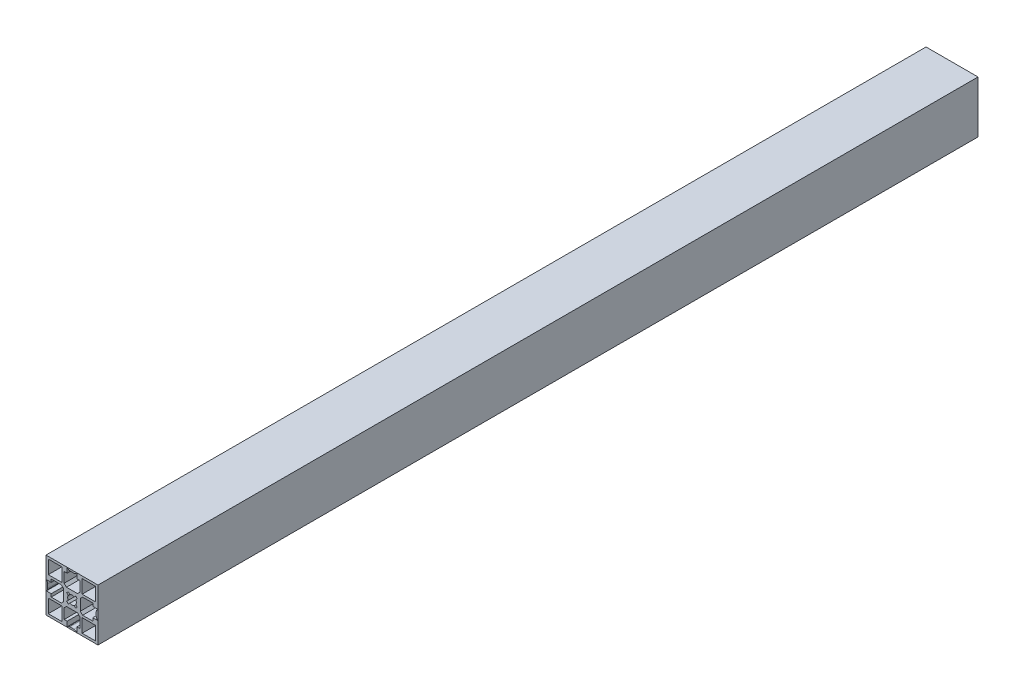
SolidWorks part; units mm, degrees
material "6061 Alloy"
ref_plane "Front Plane" through (0, 0, 0) normal (0, 0, 1) x (1, 0, 0)
ref_plane "Top Plane" through (0, 0, 0) normal (0, 1, 0) x (1, 0, 0)
ref_plane "Right Plane" through (0, 0, 0) normal (1, 0, 0) x (0, 0, -1)
sketch "Sketch1" plane through (0, 0, 0) normal (0, 0, 1) x (1, 0, 0)
  line L8 (-22.4995, -22.5007) -> (22.5005, -22.5007)
  line L9 (22.5005, -22.5007) -> (22.5005, 22.4993)
  line L10 (22.5005, 22.4993) -> (-22.4995, 22.4993)
  line L11 (-22.4995, 22.4993) -> (-22.4995, -22.5007)
  line L24 (-20.4995, -20.5007) -> (-20.4995, -8.8007)
  line L25 (-8.7996, -20.5007) -> (-20.4995, -20.5007)
  line L26 (-8.7996, -8.8007) -> (-8.7996, -20.5007)
  line L27 (-20.4995, -8.8007) -> (-8.7996, -8.8007)
  line L28 (8.8005, -20.5008) -> (8.8005, -8.8008)
  line L29 (20.5005, -20.5008) -> (8.8005, -20.5008)
  line L30 (20.5005, -8.8008) -> (20.5005, -20.5008)
  line L31 (8.8005, -8.8008) -> (20.5005, -8.8008)
  line L32 (20.5006, 8.7993) -> (8.8006, 8.7993)
  line L33 (20.5006, 20.4993) -> (20.5006, 8.7993)
  line L34 (8.8006, 20.4993) -> (20.5006, 20.4993)
  line L35 (8.8006, 8.7993) -> (8.8006, 20.4993)
  line L36 (-8.7995, 20.4993) -> (-8.7995, 8.7993)
  line L37 (-8.7995, 8.7993) -> (-20.4995, 8.7993)
  line L38 (-20.4995, 8.7993) -> (-20.4995, 20.4993)
  line L39 (-20.4995, 20.4993) -> (-8.7995, 20.4993)
  line L54 (-22.1995, -3.9507) -> (-21.7318, -3.483)
  line L55 (-22.1995, -4.2507) -> (-22.1995, -3.9507)
  line L56 (-17.9995, -4.2507) -> (-22.1995, -4.2507)
  line L57 (-17.9995, -6.8007) -> (-17.9995, -4.2507)
  line L58 (-9.1995, -6.8007) -> (-17.9995, -6.8007)
  line L59 (-7.1995, -4.8007) -> (-9.1995, -6.8007)
  line L60 (-7.1995, 4.7993) -> (-7.1995, -4.8007)
  line L61 (-9.1995, 6.7993) -> (-7.1995, 4.7993)
  line L62 (-17.9995, 6.7993) -> (-9.1995, 6.7993)
  line L63 (-17.9995, 4.2493) -> (-17.9995, 6.7993)
  line L64 (-22.1995, 4.2493) -> (-17.9995, 4.2493)
  line L65 (-22.1995, 3.9493) -> (-22.1995, 4.2493)
  line L66 (-21.7317, 3.4815) -> (-22.1995, 3.9493)
  line L67 (-20.9995, -1.7152) -> (-20.9995, 1.7137)
  line L82 (-6.7995, -18.0007) -> (-6.7995, -9.2007)
  line L83 (-4.2495, -18.0007) -> (-6.7995, -18.0007)
  line L84 (-4.2495, -22.2007) -> (-4.2495, -18.0007)
  line L85 (-3.9495, -22.2007) -> (-4.2495, -22.2007)
  line L86 (-3.4817, -21.733) -> (-3.9495, -22.2007)
  line L87 (1.715, -21.0007) -> (-1.7139, -21.0007)
  line L88 (3.9505, -22.2007) -> (3.4828, -21.733)
  line L89 (4.2505, -22.2007) -> (3.9505, -22.2007)
  line L90 (4.2505, -18.0007) -> (4.2505, -22.2007)
  line L91 (6.8005, -18.0007) -> (4.2505, -18.0007)
  line L92 (6.8005, -9.2007) -> (6.8005, -18.0007)
  line L93 (4.8005, -7.2007) -> (6.8005, -9.2007)
  line L94 (-4.7995, -7.2007) -> (4.8005, -7.2007)
  line L95 (-6.7995, -9.2007) -> (-4.7995, -7.2007)
  line L110 (7.2005, -4.8007) -> (7.2005, 4.7993)
  line L111 (9.2005, -6.8007) -> (7.2005, -4.8007)
  line L112 (18.0005, -6.8007) -> (9.2005, -6.8007)
  line L113 (18.0005, -4.2507) -> (18.0005, -6.8007)
  line L114 (22.2005, -4.2507) -> (18.0005, -4.2507)
  line L115 (22.2005, -3.9507) -> (22.2005, -4.2507)
  line L116 (21.7327, -3.4829) -> (22.2005, -3.9507)
  line L117 (21.0005, 1.7138) -> (21.0005, -1.7151)
  line L118 (22.2005, 3.9493) -> (21.7328, 3.4816)
  line L119 (22.2005, 4.2493) -> (22.2005, 3.9493)
  line L120 (18.0005, 4.2493) -> (22.2005, 4.2493)
  line L121 (18.0005, 6.7993) -> (18.0005, 4.2493)
  line L122 (9.2005, 6.7993) -> (18.0005, 6.7993)
  line L123 (7.2005, 4.7993) -> (9.2005, 6.7993)
  line L138 (-4.7995, 7.1993) -> (-6.7995, 9.1993)
  line L139 (4.8005, 7.1993) -> (-4.7995, 7.1993)
  line L140 (6.8005, 9.1993) -> (4.8005, 7.1993)
  line L141 (6.8005, 17.9993) -> (6.8005, 9.1993)
  line L142 (4.2505, 17.9993) -> (6.8005, 17.9993)
  line L143 (4.2505, 22.1993) -> (4.2505, 17.9993)
  line L144 (3.9505, 22.1993) -> (4.2505, 22.1993)
  line L145 (3.4828, 21.7316) -> (3.9505, 22.1993)
  line L146 (-1.7139, 20.9993) -> (1.715, 20.9993)
  line L147 (-3.9495, 22.1993) -> (-3.4817, 21.7315)
  line L148 (-4.2495, 22.1993) -> (-3.9495, 22.1993)
  line L149 (-4.2495, 17.9993) -> (-4.2495, 22.1993)
  line L150 (-6.7995, 17.9993) -> (-4.2495, 17.9993)
  line L151 (-6.7995, 9.1993) -> (-6.7995, 17.9993)
  line L164 (-4.5957, -3.1827) -> (-3.2622, -1.8492)
  line L165 (-3.1815, -4.5969) -> (-4.5957, -3.1827)
  line L166 (-1.848, -3.2635) -> (-3.1815, -4.5969)
  line L167 (3.1825, -4.5969) -> (1.849, -3.2635)
  line L168 (4.5967, -3.1827) -> (3.1825, -4.5969)
  line L169 (3.2633, -1.8492) -> (4.5967, -3.1827)
  line L170 (4.5967, 3.1813) -> (3.2633, 1.8478)
  line L171 (3.1825, 4.5955) -> (4.5967, 3.1813)
  line L172 (1.849, 3.262) -> (3.1825, 4.5955)
  line L173 (-3.1815, 4.5955) -> (-1.848, 3.262)
  line L174 (-4.5957, 3.1813) -> (-3.1815, 4.5955)
  line L175 (-3.2622, 1.8478) -> (-4.5957, 3.1813)
  arc A2 (-21.7318, -3.483) -> (-20.9995, -1.7152) centre (-23.4995, -1.7152) ccw
  arc A3 (-20.9995, 1.7137) -> (-21.7317, 3.4815) centre (-23.4995, 1.7137) ccw
  arc A6 (-1.7139, -21.0007) -> (-3.4817, -21.733) centre (-1.7139, -23.5007) ccw
  arc A7 (3.4828, -21.733) -> (1.715, -21.0007) centre (1.715, -23.5007) ccw
  arc A10 (21.0005, -1.7151) -> (21.7327, -3.4829) centre (23.5005, -1.7151) ccw
  arc A11 (21.7328, 3.4816) -> (21.0005, 1.7138) centre (23.5005, 1.7138) ccw
  arc A14 (1.715, 20.9993) -> (3.4828, 21.7316) centre (1.715, 23.4993) ccw
  arc A15 (-3.4817, 21.7315) -> (-1.7139, 20.9993) centre (-1.7139, 23.4993) ccw
  arc A20 (-1.848, -3.2635) -> (1.849, -3.2635) centre (0.0005, -0.0007) ccw
  arc A21 (3.2633, -1.8492) -> (3.2633, 1.8478) centre (0.0005, -0.0007) ccw
  arc A22 (1.849, 3.262) -> (-1.848, 3.262) centre (0.0005, -0.0007) ccw
  arc A23 (-3.2622, 1.8478) -> (-3.2622, -1.8492) centre (0.0005, -0.0007) ccw
extrude "Boss-Extrude1" add sketch "Sketch1" along normal blind 762 contours L10 L11 L8 L9 A23 L175 L174 L173 A22 L172 L171 L170 A21 L169 L168 L167 A20 L166 L165 L164 L24 L27 L26 L25 L28 L31 L30 L29 L32 L35 L34 L33 L38 L39 L36 L37 L67 A3 L66 L65 L64 L63 L62 L61 L60
